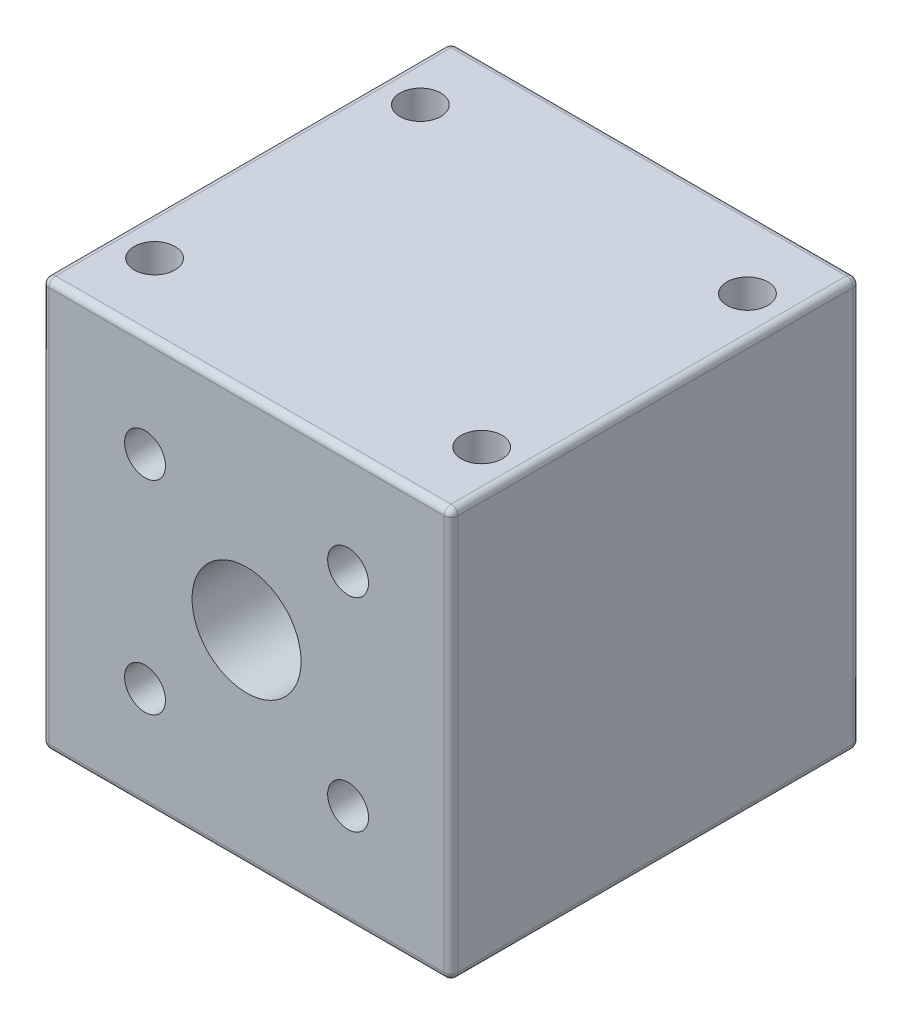
SolidWorks part; units mm, degrees
ref_plane "Alzado" through (0, 0, 0) normal (0, 0, 1) x (1, 0, 0)
ref_plane "Planta" through (0, 0, 0) normal (0, 1, 0) x (1, 0, 0)
ref_plane "Vista lateral" through (0, 0, 0) normal (1, 0, 0) x (0, 0, -1)
sketch "Croquis1" plane through (0, 0, 0) normal (0, 0, 1) x (1, 0, 0)
  line L1 (-14.5, -15) -> (14.5, -15)
  line L2 (-15, -14.5) -> (-15, 14.5)
  line L3 (-14.5, 15) -> (14.5, 15)
  line L4 (15, -14.5) -> (15, 14.5)
  line L5 (-15, -15) -> (15, 15) construction
  line L6 (-15, 15) -> (15, -15) construction
  line L7 (-7.45, -7.45) -> (7.45, -7.45) construction
  line L8 (-7.45, -7.45) -> (-7.45, 7.45) construction
  line L9 (-7.45, 7.45) -> (7.45, 7.45) construction
  line L10 (7.45, -7.45) -> (7.45, 7.45) construction
  line L11 (-7.45, -7.45) -> (7.45, 7.45) construction
  line L12 (-7.45, 7.45) -> (7.45, -7.45) construction
  circle A0 centre (0, 0) radius 4
  circle A1 centre (-7.45, 7.45) radius 1.5
  circle A2 centre (7.45, 7.45) radius 1.5
  circle A3 centre (-7.45, -7.45) radius 1.5
  circle A4 centre (7.45, -7.45) radius 1.5
  arc A5 (-14.5, -15) -> (-15, -14.5) centre (-14.5, -14.5) cw
  arc A6 (14.5, -15) -> (15, -14.5) centre (14.5, -14.5) ccw
  arc A7 (14.5, 15) -> (15, 14.5) centre (14.5, 14.5) cw
  arc A8 (-15, 14.5) -> (-14.5, 15) centre (-14.5, 14.5) cw
  point P0 (0, 0)
  dimension "D3" = 8
  dimension "D6" = 3
  dimension "D7" = 3
  dimension "D8" = 3
  dimension "D9" = 3
  dimension "D10" = 0.5
  dimension "D1" = 30
  dimension "D2" = 30
  dimension "D4" = 14.9
  dimension "D5" = 14.9
extrude "Saliente-Extruir1" add sketch "Croquis1" along normal blind 30
sketch "Croquis2" plane through (0, -15, 0) normal (0, -1, 0) x (1, 0, 0)
  line L0 (0, 30) -> (0, 0) construction
  line L1 (-14.5, 30) -> (14.5, 30) construction
  line L2 (-15, 15) -> (15, 15) construction
  line L3 (-15, 30) -> (-15, 0) construction
  line L4 (15, 30) -> (15, 0) construction
  line L6 (-12, 5.25) -> (12, 5.25) construction
  line L7 (-12, 5.25) -> (-12, 24.75) construction
  line L8 (-12, 24.75) -> (12, 24.75) construction
  line L9 (12, 5.25) -> (12, 24.75) construction
  line L10 (-12, 5.25) -> (12, 24.75) construction
  line L11 (-12, 24.75) -> (12, 5.25) construction
  circle A0 centre (-12, 24.75) radius 1.5
  circle A1 centre (12, 24.75) radius 1.5
  circle A2 centre (12, 5.25) radius 1.5
  circle A3 centre (-12, 5.25) radius 1.5
  point P11 (0, 15)
  dimension "D3" = 3
  dimension "D4" = 3
  dimension "D5" = 3
  dimension "D6" = 3
  dimension "D1" = 19.5
  dimension "D2" = 24
extrude "Cortar-Extruir1" cut sketch "Croquis2" against normal blind 30
fillet "Redondeo1" radius 0.5 8 edges at (14.8536, -14.8536, 30) (15, 0, 30) (14.8536, 14.8536, 30) (0, 15, 30) (-14.8536, 14.8536, 30) (-15, 0, 30) (-14.8536, -14.8536, 30) (0, -15, 30)
fillet "Redondeo2" radius 0.5 8 edges at (15, 0, 0) (14.8536, -14.8536, 0) (0, -15, 0) (-14.8536, -14.8536, 0) (-15, 0, 0) (-14.8536, 14.8536, 0) (0, 15, 0) (14.8536, 14.8536, 0)
